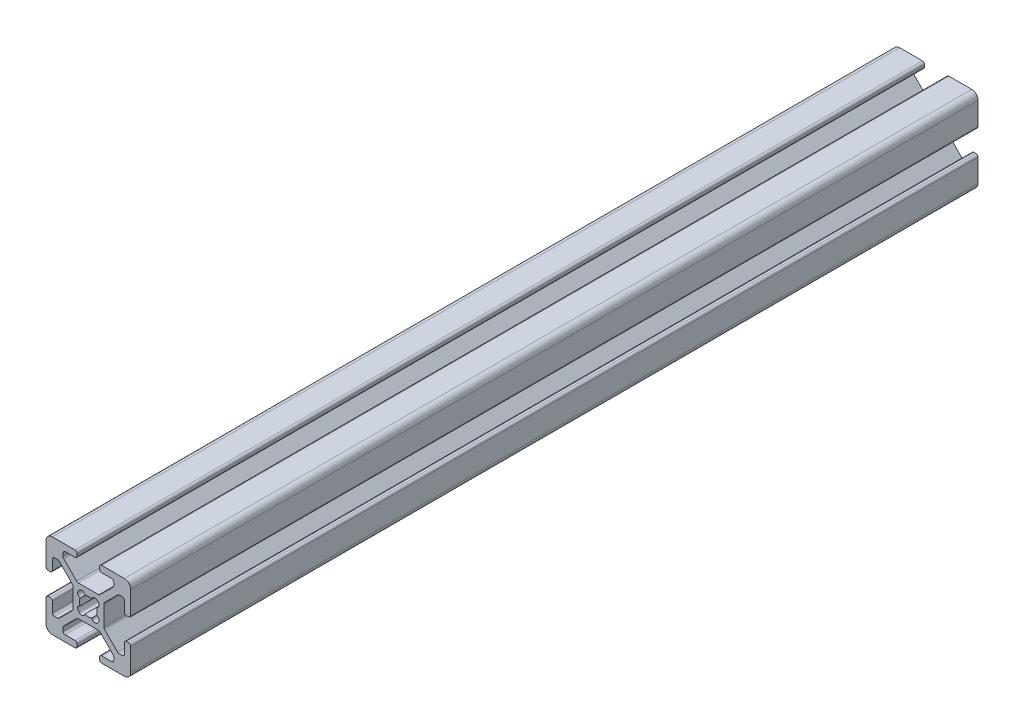
SolidWorks part; units mm, degrees
ref_plane "Front Plane" through (0, 0, 0) normal (0, 0, 1) x (1, 0, 0)
ref_plane "Top Plane" through (0, 0, 0) normal (0, 1, 0) x (1, 0, 0)
ref_plane "Right Plane" through (0, 0, 0) normal (1, 0, 0) x (0, 0, -1)
sketch "Sketch1" plane through (0, 0, 0) normal (0, 0, 1) x (1, 0, 0)
  line L0 (-5.0323, -0.3411) -> (-5.5163, -0.3411)
  line L1 (-6.0243, 0.1669) -> (-6.0243, 2.5159)
  line L2 (-4.5243, 0.1669) -> (-4.5243, 5.5289)
  line L3 (-10.8693, -5.355) -> (-10.8693, -0.5871)
  line L4 (-7.2582, 3.0239) -> (-6.5323, 3.0239)
  line L5 (-7.6174, 2.8752) -> (-10.7205, -0.2279)
  line L6 (-5.0323, -5.6011) -> (-5.5163, -5.6011)
  line L7 (-4.5243, -6.1091) -> (-4.5243, -11.4711)
  line L8 (-6.0243, -6.1091) -> (-6.0243, -8.4581)
  line L9 (-7.2582, -8.9661) -> (-6.5323, -8.9661)
  line L10 (-7.6174, -8.8173) -> (-10.7205, -5.7142)
  line L11 (-12.3994, -5.2756) -> (-12.2198, -5.096)
  line L12 (-17.1543, 6.5209) -> (-17.1543, 6.0369)
  line L13 (-17.6623, 7.0289) -> (-23.0243, 7.0289)
  line L14 (-17.6623, 5.5289) -> (-20.0113, 5.5289)
  line L15 (-12.1404, 0.6839) -> (-16.9082, 0.6839)
  line L16 (-20.5193, 4.295) -> (-20.5193, 5.0209)
  line L17 (-20.3705, 3.9358) -> (-17.2674, 0.8327)
  line L18 (-11.8943, 6.5209) -> (-11.8943, 6.0369)
  line L19 (-11.3863, 7.0289) -> (-6.0243, 7.0289)
  line L20 (-11.3863, 5.5289) -> (-9.0373, 5.5289)
  line L21 (-8.5293, 4.295) -> (-8.5293, 5.0209)
  line L22 (-8.6781, 3.9358) -> (-11.7812, 0.8327)
  line L23 (-12.2198, -0.8462) -> (-12.3994, -0.6666)
  line L24 (-24.0163, -5.6011) -> (-23.5323, -5.6011)
  line L25 (-24.5243, -6.1091) -> (-24.5243, -11.4711)
  line L26 (-23.0243, -6.1091) -> (-23.0243, -8.4581)
  line L27 (-18.1793, -0.5871) -> (-18.1793, -5.355)
  line L28 (-21.7904, -8.9661) -> (-22.5163, -8.9661)
  line L29 (-21.4312, -8.8173) -> (-18.3281, -5.7142)
  line L30 (-24.0163, -0.3411) -> (-23.5323, -0.3411)
  line L31 (-24.5243, 0.1669) -> (-24.5243, 5.5289)
  line L32 (-23.0243, 0.1669) -> (-23.0243, 2.5159)
  line L33 (-21.7904, 3.0239) -> (-22.5163, 3.0239)
  line L34 (-21.4312, 2.8752) -> (-18.3281, -0.2279)
  line L35 (-16.6492, -0.6666) -> (-16.8288, -0.8462)
  line L36 (-11.8943, -12.4631) -> (-11.8943, -11.9791)
  line L37 (-11.3863, -12.9711) -> (-6.0243, -12.9711)
  line L38 (-11.3863, -11.4711) -> (-9.0373, -11.4711)
  line L39 (-16.9082, -6.6261) -> (-12.1404, -6.6261)
  line L40 (-8.5293, -10.2371) -> (-8.5293, -10.9631)
  line L41 (-8.6781, -9.8779) -> (-11.7812, -6.7748)
  line L42 (-17.1543, -12.4631) -> (-17.1543, -11.9791)
  line L43 (-17.6623, -12.9711) -> (-23.0243, -12.9711)
  line L44 (-17.6623, -11.4711) -> (-20.0113, -11.4711)
  line L45 (-20.5193, -10.2371) -> (-20.5193, -10.9631)
  line L46 (-20.3705, -9.8779) -> (-17.2674, -6.7748)
  line L47 (-16.8288, -5.096) -> (-16.6492, -5.2756)
  arc A0 (-15.3283, -4.9062) -> (-13.7203, -4.9062) centre (-14.5243, -2.9711) ccw
  arc A1 (-6.0243, 2.5159) -> (-6.5323, 3.0239) centre (-6.5323, 2.5159) ccw
  arc A2 (-7.2582, 3.0239) -> (-7.6174, 2.8752) centre (-7.2582, 2.5159) ccw
  arc A3 (-10.7205, -0.2279) -> (-10.8693, -0.5871) centre (-10.3613, -0.5871) ccw
  arc A4 (-10.8693, -5.355) -> (-10.7205, -5.7142) centre (-10.3613, -5.355) ccw
  arc A5 (-7.6174, -8.8173) -> (-7.2582, -8.9661) centre (-7.2582, -8.4581) ccw
  arc A6 (-6.5323, -8.9661) -> (-6.0243, -8.4581) centre (-6.5323, -8.4581) ccw
  arc A7 (-5.5163, -5.6011) -> (-6.0243, -6.1091) centre (-5.5163, -6.1091) ccw
  arc A8 (-4.5243, -6.1091) -> (-5.0323, -5.6011) centre (-5.0323, -6.1091) ccw
  arc A9 (-5.0323, -0.3411) -> (-4.5243, 0.1669) centre (-5.0323, 0.1669) ccw
  arc A10 (-6.0243, 0.1669) -> (-5.5163, -0.3411) centre (-5.5163, 0.1669) ccw
  arc A11 (-13.7203, -4.9062) -> (-12.3994, -5.2756) centre (-12.9559, -4.7191) ccw
  arc A12 (-12.2198, -5.096) -> (-12.5892, -3.775) centre (-12.7763, -4.5395) ccw
  arc A13 (-17.1543, 6.5209) -> (-17.6623, 7.0289) centre (-17.6623, 6.5209) ccw
  arc A14 (-17.6623, 5.5289) -> (-17.1543, 6.0369) centre (-17.6623, 6.0369) ccw
  arc A15 (-12.5892, -3.775) -> (-12.5892, -2.1671) centre (-14.5243, -2.9711) ccw
  arc A16 (-17.2674, 0.8327) -> (-16.9082, 0.6839) centre (-16.9082, 1.1919) ccw
  arc A17 (-20.0113, 5.5289) -> (-20.5193, 5.0209) centre (-20.0113, 5.0209) ccw
  arc A18 (-20.5193, 4.295) -> (-20.3705, 3.9358) centre (-20.0113, 4.295) ccw
  arc A19 (-11.8943, 6.0369) -> (-11.3863, 5.5289) centre (-11.3863, 6.0369) ccw
  arc A20 (-11.3863, 7.0289) -> (-11.8943, 6.5209) centre (-11.3863, 6.5209) ccw
  arc A21 (-8.5293, 5.0209) -> (-9.0373, 5.5289) centre (-9.0373, 5.0209) ccw
  arc A22 (-8.6781, 3.9358) -> (-8.5293, 4.295) centre (-9.0373, 4.295) ccw
  arc A23 (-12.1404, 0.6839) -> (-11.7812, 0.8327) centre (-12.1404, 1.1919) ccw
  arc A24 (-12.5892, -2.1671) -> (-12.2198, -0.8462) centre (-12.7763, -1.4027) ccw
  arc A25 (-12.3994, -0.6666) -> (-13.7203, -1.0359) centre (-12.9559, -1.223) ccw
  arc A26 (-24.0163, -5.6011) -> (-24.5243, -6.1091) centre (-24.0163, -6.1091) ccw
  arc A27 (-23.0243, -6.1091) -> (-23.5323, -5.6011) centre (-23.5323, -6.1091) ccw
  arc A28 (-13.7203, -1.0359) -> (-15.3283, -1.0359) centre (-14.5243, -2.9711) ccw
  arc A29 (-18.3281, -5.7142) -> (-18.1793, -5.355) centre (-18.6873, -5.355) ccw
  arc A30 (-23.0243, -8.4581) -> (-22.5163, -8.9661) centre (-22.5163, -8.4581) ccw
  arc A31 (-21.7904, -8.9661) -> (-21.4312, -8.8173) centre (-21.7904, -8.4581) ccw
  arc A32 (-23.5323, -0.3411) -> (-23.0243, 0.1669) centre (-23.5323, 0.1669) ccw
  arc A33 (-24.5243, 0.1669) -> (-24.0163, -0.3411) centre (-24.0163, 0.1669) ccw
  arc A34 (-22.5163, 3.0239) -> (-23.0243, 2.5159) centre (-22.5163, 2.5159) ccw
  arc A35 (-21.4312, 2.8752) -> (-21.7904, 3.0239) centre (-21.7904, 2.5159) ccw
  arc A36 (-18.1793, -0.5871) -> (-18.3281, -0.2279) centre (-18.6873, -0.5871) ccw
  arc A37 (-15.3283, -1.0359) -> (-16.6492, -0.6666) centre (-16.0927, -1.223) ccw
  arc A38 (-16.8288, -0.8462) -> (-16.4594, -2.1671) centre (-16.2723, -1.4027) ccw
  arc A39 (-11.8943, -12.4631) -> (-11.3863, -12.9711) centre (-11.3863, -12.4631) ccw
  arc A40 (-11.3863, -11.4711) -> (-11.8943, -11.9791) centre (-11.3863, -11.9791) ccw
  arc A41 (-16.4594, -2.1671) -> (-16.4594, -3.775) centre (-14.5243, -2.9711) ccw
  arc A42 (-11.7812, -6.7748) -> (-12.1404, -6.6261) centre (-12.1404, -7.1341) ccw
  arc A43 (-9.0373, -11.4711) -> (-8.5293, -10.9631) centre (-9.0373, -10.9631) ccw
  arc A44 (-8.5293, -10.2371) -> (-8.6781, -9.8779) centre (-9.0373, -10.2371) ccw
  arc A45 (-17.1543, -11.9791) -> (-17.6623, -11.4711) centre (-17.6623, -11.9791) ccw
  arc A46 (-17.6623, -12.9711) -> (-17.1543, -12.4631) centre (-17.6623, -12.4631) ccw
  arc A47 (-20.5193, -10.9631) -> (-20.0113, -11.4711) centre (-20.0113, -10.9631) ccw
  arc A48 (-20.3705, -9.8779) -> (-20.5193, -10.2371) centre (-20.0113, -10.2371) ccw
  arc A49 (-16.9082, -6.6261) -> (-17.2674, -6.7748) centre (-16.9082, -7.1341) ccw
  arc A50 (-16.4594, -3.775) -> (-16.8288, -5.096) centre (-16.2723, -4.5395) ccw
  arc A51 (-16.6492, -5.2756) -> (-15.3283, -4.9062) centre (-16.0927, -4.7191) ccw
  arc A52 (-4.5243, 5.5289) -> (-6.0243, 7.0289) centre (-6.0243, 5.5289) ccw
  arc A53 (-6.0243, -12.9711) -> (-4.5243, -11.4711) centre (-6.0243, -11.4711) ccw
  arc A54 (-24.5243, -11.4711) -> (-23.0243, -12.9711) centre (-23.0243, -11.4711) ccw
  arc A55 (-23.0243, 7.0289) -> (-24.5243, 5.5289) centre (-23.0243, 5.5289) ccw
extrude "Extrude1" add sketch "Sketch1" along normal blind 200
